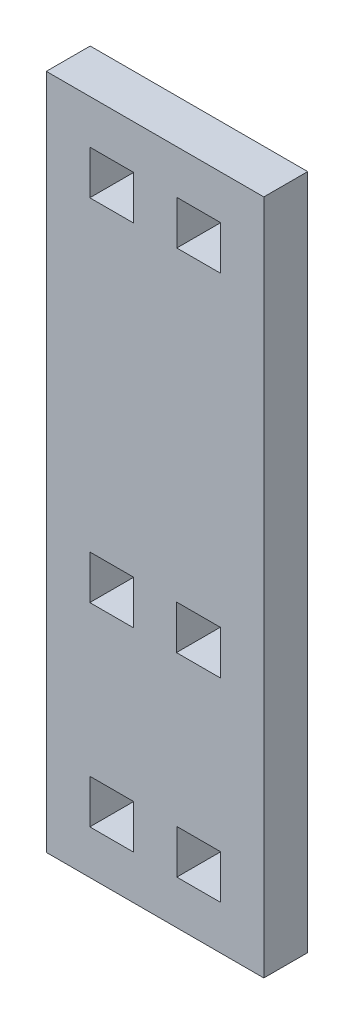
SolidWorks part; units mm, degrees
ref_plane "Front Plane" through (0, 0, 0) normal (0, 0, 1) x (1, 0, 0)
ref_plane "Top Plane" through (0, 0, 0) normal (0, 1, 0) x (1, 0, 0)
ref_plane "Right Plane" through (0, 0, 0) normal (1, 0, 0) x (0, 0, -1)
sketch "Sketch1" plane through (0, 0, 0) normal (0, 0, 1) x (1, 0, 0)
  line L1 (0, 0) -> (25.53, 0)
  line L2 (0, 0) -> (0, 79.4)
  line L3 (0, 79.4) -> (25.53, 79.4)
  line L4 (25.53, 0) -> (25.53, 79.4)
  dimension "D1" = 79.4
  dimension "D2" = 25.53
extrude "Boss-Extrude1" add sketch "Sketch1" along normal blind 5.15
sketch "Sketch2" plane through (0, 0, 5.15) normal (0, 0, 1) x (1, 0, 0)
  line L0 (25.53, 39.7) -> (-17.1954, 39.7) construction
  line L1 (2.8325, 0) -> (-2.8325, 0) construction
  line L2 (20.424, 69.3685) -> (25.53, 69.3685) construction
  line L3 (5.106, 74.25) -> (10.212, 74.25)
  line L4 (5.106, 74.25) -> (5.106, 69.1)
  line L5 (5.106, 69.1) -> (10.212, 69.1)
  line L6 (10.212, 74.25) -> (10.212, 69.1)
  line L7 (15.318, 74.25) -> (20.424, 74.25)
  line L8 (15.318, 74.25) -> (15.318, 69.1)
  line L9 (15.318, 69.1) -> (20.424, 69.1)
  line L10 (20.424, 74.25) -> (20.424, 69.1)
  line L11 (25.53, 0) -> (25.53, 79.4) construction
  line L12 (10.212, 71.2882) -> (15.318, 71.2882) construction
  line L13 (5.106, 70.4299) -> (0, 70.4299) construction
  line L14 (0, -2.8325) -> (0, 2.8325) construction
  line L15 (25.53, 79.4) -> (0, 79.4) construction
  line L16 (5.106, 33.1) -> (10.256, 33.1)
  line L17 (5.106, 33.1) -> (5.106, 27.95)
  line L18 (5.106, 27.95) -> (10.256, 27.95)
  line L19 (10.256, 33.1) -> (10.256, 27.95)
  line L20 (15.274, 33.1) -> (20.424, 33.1)
  line L21 (15.274, 33.1) -> (15.274, 27.95)
  line L22 (15.274, 27.95) -> (20.424, 27.95)
  line L23 (20.424, 33.1) -> (20.424, 27.95)
  line L24 (20.424, 71.675) -> (25.53, 71.675) construction
  line L44 (20.424, 5.15) -> (20.424, 10.3)
  line L45 (15.318, 10.3) -> (20.424, 10.3)
  line L46 (15.318, 5.15) -> (20.424, 5.15)
  line L47 (10.212, 5.15) -> (10.212, 10.3)
  line L48 (5.106, 5.15) -> (10.212, 5.15)
  line L49 (5.106, 5.15) -> (5.106, 10.3)
  line L50 (5.106, 10.3) -> (10.212, 10.3)
  line L51 (15.318, 5.15) -> (15.318, 10.3)
  dimension "D1" = 5.15
  dimension "D2" = 5.15
  dimension "D3" = 5.15
  dimension "D4" = 5.15
  dimension "D5" = 5.15
  dimension "D6" = 36
extrude "Cut-Extrude1" cut sketch "Sketch2" against normal through all
